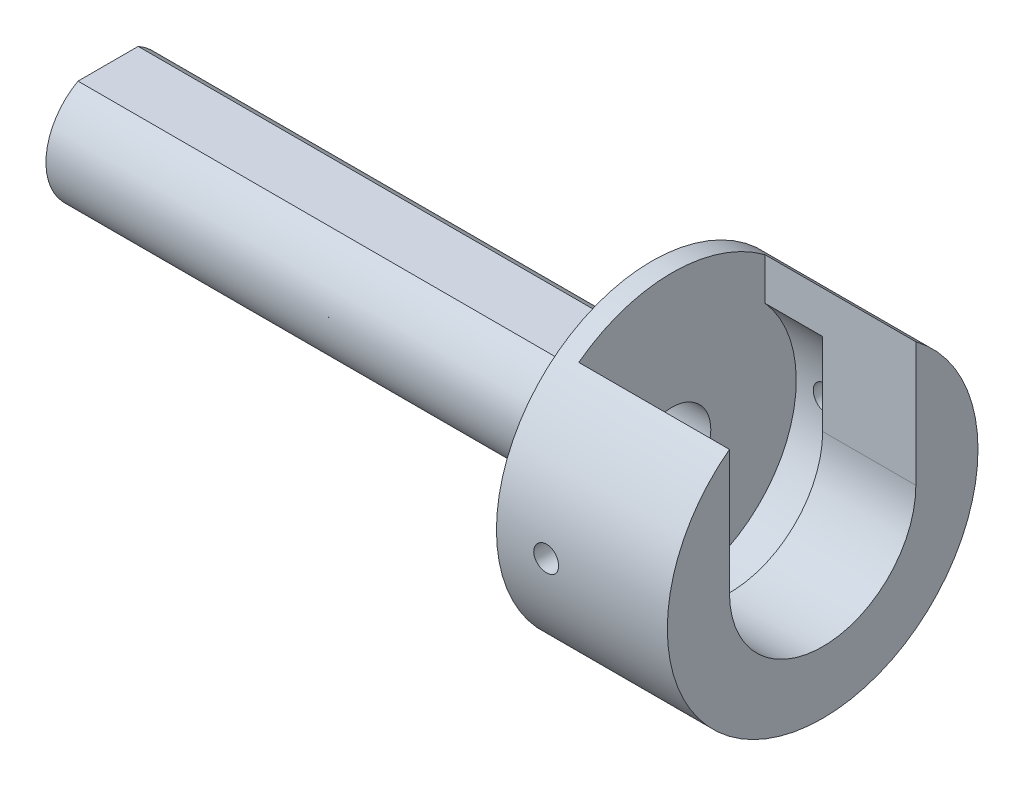
SolidWorks part; units mm, degrees
ref_plane "Front Plane" through (0, 0, 0) normal (0, 0, 1) x (1, 0, 0)
ref_plane "Top Plane" through (0, 0, 0) normal (0, 1, 0) x (1, 0, 0)
ref_plane "Right Plane" through (0, 0, 0) normal (1, 0, 0) x (0, 0, -1)
sketch "Sketch1" plane through (0, 0, 0) normal (1, 0, 0) x (0, 0, -1)
  circle A0 centre (0, 0) radius 10
  dimension "D1" = 20
extrude "Boss-Extrude1" add sketch "Sketch1" along normal blind 11
sketch "Sketch3" plane through (11, 0, 0) normal (1, 0, 0) x (0, 0, -1)
  line L0 (-6, 0) -> (-6, 8)
  line L1 (6, 0) -> (6, 8)
  arc A0 (-6, 0) -> (6, 0) centre (0, 0) ccw
  arc A2 (6, 8) -> (-6, 8) centre (0, 0) ccw
  dimension "D1" = 12
  dimension "D2" = 20
extrude "Cut-Extrude2" cut sketch "Sketch3" against normal blind 9.7
sketch "Sketch4" plane through (1.3, 0, 0) normal (1, 0, 0) x (0, 0, -1)
  circle A0 centre (0, 0) radius 8
  dimension "D1" = 16
extrude "Cut-Extrude3" cut sketch "Sketch4" along normal blind 3.7
sketch "Sketch24" plane through (0, 0, 0) normal (-1, 0, 0) x (0, 0, 1)
  line L0 (-1.9365, 3.5) -> (1.9365, 3.5)
  arc A0 (-1.9365, 3.5) -> (1.9365, 3.5) centre (0, 0) ccw
  dimension "D1" = 8
  dimension "D2" = 3.5
extrude "Boss-Extrude2" add sketch "Sketch24" along normal blind 35
sketch "Sketch2" plane through (0, 0, 0) normal (-1, 0, 0) x (0, 0, 1)
  circle A0 centre (0, 0) radius 2.5
  dimension "D1" = 5
extrude "Cut-Extrude1" cut sketch "Sketch2" against normal through all both and the other way through all
ref_plane "Plane1" through (0, 0, -10) normal (0, 0, 1) x (1, 0, 0)
hole_wizard "M2x0.4 Tapped Hole1" positions "Sketch22" profile "Sketch23" tap size "M2x0.4" standard "ANSI Metric"
sketch "Sketch22" plane through (0, 0, -10) normal (0, 0, 1) x (1, 0, 0)
  line L0 (0, 0) -> (36.8629, 0) construction
  line L2 (11, -10) -> (11, 8) construction
  point P0 (3.2, 0)
  dimension "D1" = 7.8
sketch "Sketch23" plane through (3.2, 0, -10) normal (1, 0, 0) x (0, 1, 0)
  line L0 (0, 0) -> (0, 2)
  line L1 (0, 2) -> (0.8, 2)
  line L2 (0.8, 2) -> (0.8, 0)
  line L5 (0.8, 0) -> (0, 0)
  line L11 (0, -6.35) -> (0, 107.95) construction
  dimension "Thru Tap Drill Dia." = 1.6
  dimension "Thru Tap Drill Depth" = 2
cosmetic thread "Hole Thread10" parameters "D1"=2.0401, "D2"=2
ref_plane "Plane2" through (0, 0, 10) normal (0, 0, 1) x (1, 0, 0)
hole_wizard "M2x0.4 Tapped Hole2" positions "Sketch12" profile "Sketch13" tap size "M2x0.4" standard "ANSI Metric"
sketch "Sketch12" plane through (0, 0, 10) normal (0, 0, 1) x (1, 0, 0)
  line L0 (11, -10) -> (11, 8) construction
  line L2 (0, 0) -> (39.7675, 0) construction
  point P0 (3.2, 0)
  dimension "D1" = 7.8
sketch "Sketch13" plane through (3.2, 0, 10) normal (1, 0, 0) x (0, -1, 0)
  line L0 (0, 0) -> (0, 2)
  line L1 (0, 2) -> (0.8, 2)
  line L2 (0.8, 2) -> (0.8, 0)
  line L5 (0.8, 0) -> (0, 0)
  line L11 (0, -6.35) -> (0, 107.95) construction
  dimension "Thru Tap Drill Dia." = 1.6
  dimension "Thru Tap Drill Depth" = 2
cosmetic thread "Hole Thread11" parameters "D1"=2.0401, "D2"=2
ref_plane "Plane3" through (0, -10, 0) normal (0, 1, 0) x (1, 0, 0)
hole_wizard "M2x0.4 Tapped Hole3" positions "Sketch25" profile "Sketch26" tap size "M2x0.4" standard "ANSI Metric"
sketch "Sketch25" plane through (0, -10, 0) normal (0, 1, 0) x (1, 0, 0)
  line L0 (0, 10) -> (0, -10) construction
  point P0 (3, 0)
  dimension "D1" = 3
sketch "Sketch26" plane through (3, -10, 0) normal (1, 0, 0) x (0, 0, -1)
  line L0 (0, 0) -> (0, 2)
  line L1 (0, 2) -> (0.8, 2)
  line L2 (0.8, 2) -> (0.8, 0)
  line L5 (0.8, 0) -> (0, 0)
  line L11 (0, -6.35) -> (0, 107.95) construction
  dimension "Thru Tap Drill Dia." = 1.6
  dimension "Thru Tap Drill Depth" = 2
cosmetic thread "Hole Thread12" parameters "D1"=2.0401, "D2"=2
